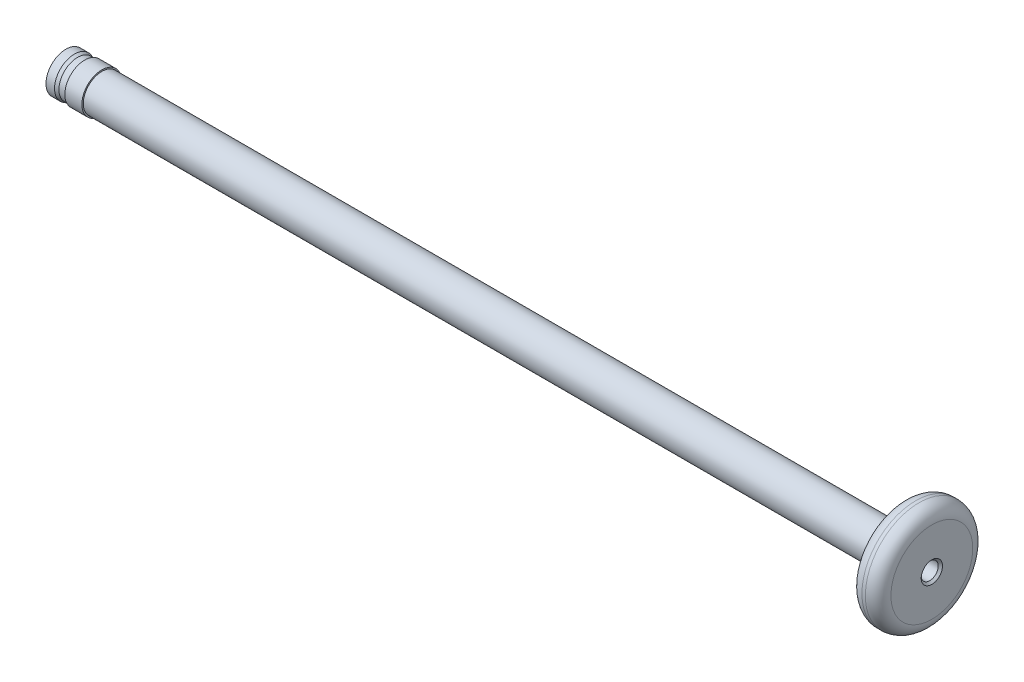
SolidWorks part; units mm, degrees
ref_plane "Front Plane" through (0, 0, 0) normal (0, 0, 1) x (1, 0, 0)
ref_plane "Top Plane" through (0, 0, 0) normal (0, 1, 0) x (1, 0, 0)
ref_plane "Right Plane" through (0, 0, 0) normal (1, 0, 0) x (0, 0, -1)
sketch "Sketch1" plane through (0, 0, 0) normal (0, 0, 1) x (1, 0, 0)
  line L0 (-50.8, 0) -> (50.8, 0) construction
  line L1 (-50.8, 2.185) -> (50.8, 2.185) construction
  line L2 (-50.8, 2.185) -> (-50.8, -2.185) construction
  line L3 (-50.8, -2.185) -> (50.8, -2.185) construction
  line L4 (50.8, 2.185) -> (50.8, -2.185) construction
  line L5 (-50.8, 2.185) -> (50.8, -2.185) construction
  line L6 (-50.8, -2.185) -> (50.8, 2.185) construction
  line L7 (-50.8, 2.185) -> (-50.7869, 2.335) construction
  line L8 (-50.7869, 2.335) -> (-49.7869, 2.335) construction
  line L9 (-49.7869, 2.335) -> (-49.42, 2.185) construction
  line L10 (-48.59, 2.185) -> (-48.5769, 2.335) construction
  line L11 (-48.5769, 2.335) -> (-46.5769, 2.335) construction
  line L12 (-46.5769, 2.335) -> (-46.5638, 2.185) construction
  line L13 (-49.42, 2.185) -> (-48.59, 2.185)
  line L14 (50.8, 0) -> (47.4, 0) construction
  line L15 (47.4, 6.3) -> (50.8, 6.3) construction
  line L16 (47.4, 6.3) -> (47.4, -6.3) construction
  line L17 (47.4, -6.3) -> (50.8, -6.3) construction
  line L18 (50.8, 6.3) -> (50.8, -6.3) construction
  line L19 (-50.8, 2.185) -> (-50.7869, 2.335)
  line L20 (-50.7869, 2.335) -> (-49.7869, 2.335)
  line L21 (-49.7869, 2.335) -> (-49.42, 2.185)
  line L22 (-46.5638, 2.185) -> (-46.5769, 2.335)
  line L23 (-48.59, 2.185) -> (-48.5769, 2.335)
  line L24 (-48.5769, 2.335) -> (-46.5769, 2.335)
  line L25 (47.4, 2.185) -> (-46.5638, 2.185)
  line L26 (47.4, 2.185) -> (47.4, 6.3)
  line L27 (47.4, 6.3) -> (50.8, 6.3)
  line L28 (-50.8, 2.185) -> (-50.8, 0)
  line L29 (-50.8, 0) -> (50.8, 0)
  line L30 (50.8, 0) -> (50.8, 6.3)
  point P0 (0, 0)
  point P13 (-50.2869, 2.335)
  dimension "D1" = 101.6
  dimension "D2" = 4.37
  dimension "D3" = 0.15
  dimension "D4" = 1.38
  dimension "D5" = 1
  dimension "D6" = 85
  dimension "D7" = 0.83
  dimension "D8" = 2
  dimension "D9" = 85
  dimension "D10" = 85
  dimension "D11" = 12.6
  dimension "D12" = 3.4
revolve "Revolve1" add sketch "Sketch1" angle 360 about L29
sketch "Sketch2" plane through (50.8, 0, 0) normal (1, 0, 0) x (0, 0, -1)
  circle A0 centre (0, 0) radius 1
  dimension "D1" = 2
extrude "Cut-Extrude1" cut sketch "Sketch2" against normal blind 5
fillet "Fillet1" radius 1.5 2 edges at (47.4, -6.3, 0) (50.8, -6.3, 0)
chamfer "Chamfer1" distance 0.25 angle 45 1 edges at (50.8, 1, 0)
